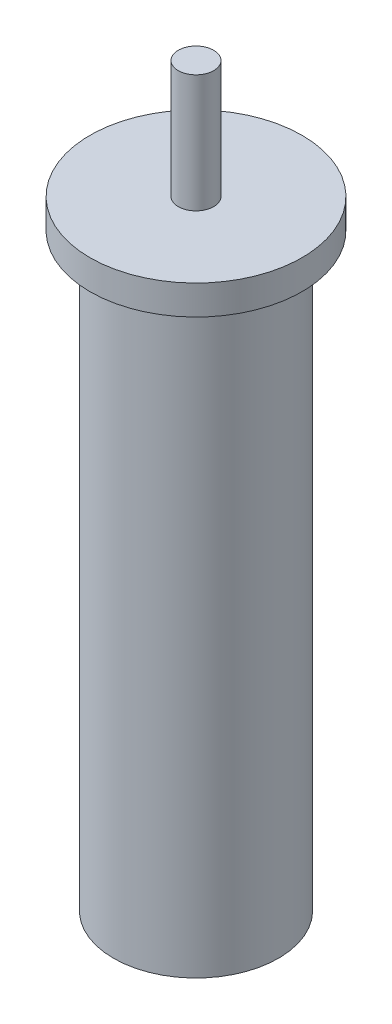
SolidWorks part; units mm, degrees
ref_plane "Front Plane" through (0, 0, 0) normal (0, 0, 1) x (1, 0, 0)
ref_plane "Top Plane" through (0, 0, 0) normal (0, 1, 0) x (1, 0, 0)
ref_plane "Right Plane" through (0, 0, 0) normal (1, 0, 0) x (0, 0, -1)
sketch "Sketch1" plane through (0, 0, 0) normal (0, 1, 0) x (1, 0, 0)
  circle A0 centre (0, 0) radius 14
  dimension "D1" = 28
extrude "Boss-Extrude1" add sketch "Sketch1" along normal blind 100
sketch "Sketch2" plane through (0, 100, 0) normal (0, 1, 0) x (1, 0, 0)
  circle A0 centre (0, 0) radius 18
  dimension "D1" = 36
extrude "Boss-Extrude2" add sketch "Sketch2" along normal blind 5
sketch "Sketch3" plane through (0, 105, 0) normal (0, 1, 0) x (1, 0, 0)
  circle A0 centre (0, 0) radius 3
  dimension "D1" = 6
extrude "Boss-Extrude3" add sketch "Sketch3" along normal blind 20
